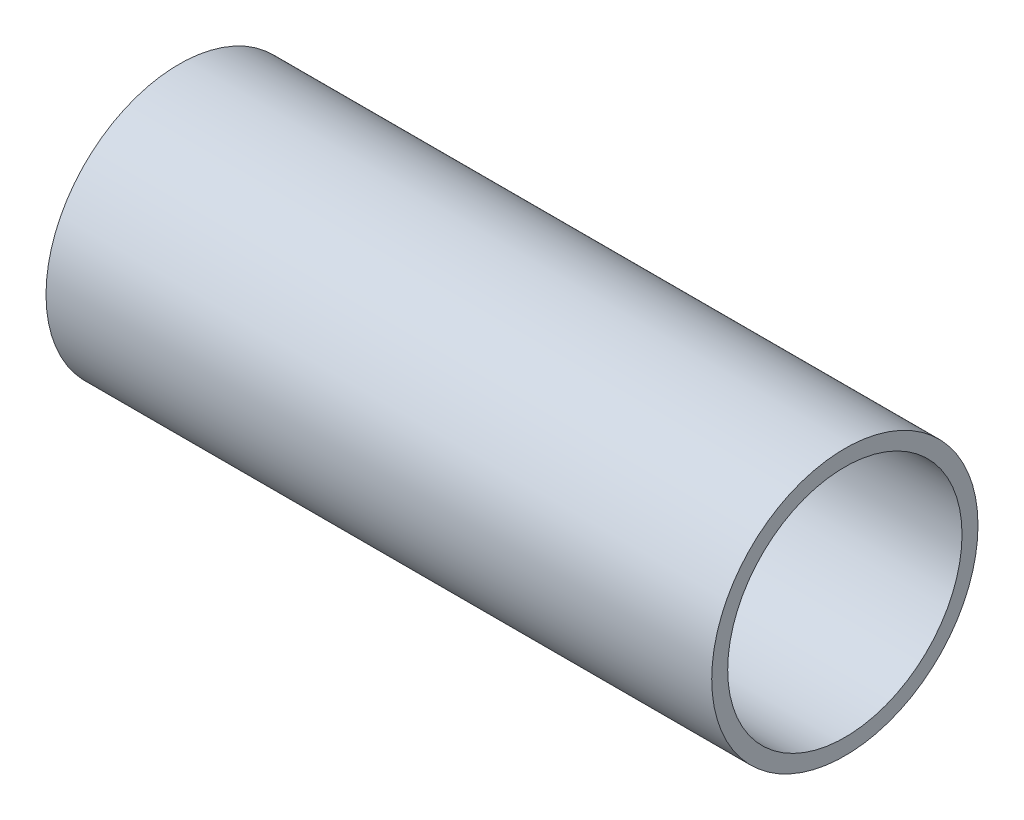
SolidWorks part; units mm, degrees
ref_plane "前基準面" through (0, 0, 0) normal (0, 0, 1) x (1, 0, 0)
ref_plane "上基準面" through (0, 0, 0) normal (0, 1, 0) x (1, 0, 0)
ref_plane "右基準面" through (0, 0, 0) normal (1, 0, 0) x (0, 0, -1)
sketch "草圖1" plane through (0, 0, 0) normal (1, 0, 0) x (0, 0, -1)
  circle A0 centre (-1.3966, 0) radius 25
  circle A1 centre (-1.3966, 0) radius 22
  dimension "D1" = 50
  dimension "D2" = 44
extrude "填料-伸長1" add sketch "草圖1" along normal blind 125
